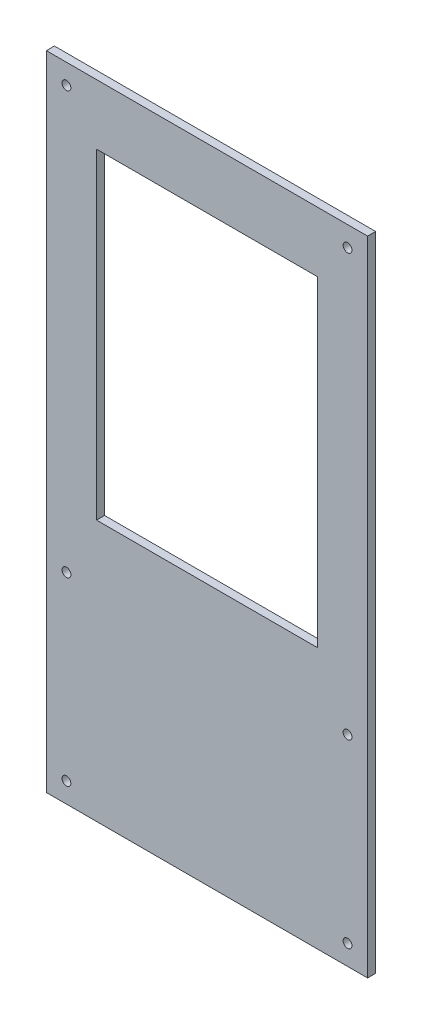
SolidWorks part; units mm, degrees
ref_plane "Plan de face" through (0, 0, 0) normal (0, 0, 1) x (1, 0, 0)
ref_plane "Plan de dessus" through (0, 0, 0) normal (0, 1, 0) x (1, 0, 0)
ref_plane "Plan de droite" through (0, 0, 0) normal (1, 0, 0) x (0, 0, -1)
sketch "Esquisse1" plane through (0, 0, 0) normal (0, 0, 1) x (1, 0, 0)
  line L0 (0, 220) -> (0, 0) construction
  line L1 (80, 220) -> (-80, 220)
  line L2 (80, 220) -> (80, -220)
  line L3 (80, -220) -> (-80, -220)
  line L4 (-80, 220) -> (-80, -220)
  line L5 (80, 220) -> (-80, -220) construction
  line L6 (80, -220) -> (-80, 220) construction
  line L7 (0, 0) -> (80, 0) construction
  line L8 (-70, 220) -> (-70, -220) construction
  line L9 (-70, -220) -> (-80, -210) construction
  line L10 (-80, -210) -> (80, -210) construction
  line L11 (-80, 210) -> (80, 210) construction
  line L12 (70, 220) -> (70, -220) construction
  line L14 (-55, 190) -> (55, 190)
  line L15 (-55, 190) -> (-55, 30)
  line L16 (-55, 30) -> (55, 30)
  line L17 (55, 190) -> (55, 30)
  line L18 (-55, 190) -> (55, 30) construction
  line L19 (-55, 30) -> (55, 190) construction
  circle A0 centre (70, 0) radius 2.2
  circle A1 centre (70, 210) radius 2.2
  circle A2 centre (70, -210) radius 2.2
  circle A3 centre (-70, 210) radius 2.2
  circle A4 centre (-70, 0) radius 2.2
  circle A5 centre (-70, -210) radius 2.2
  point P0 (0, 0)
  point P29 (0, 110)
  dimension "D5" = 4.4
  dimension "D6" = 4.4
  dimension "D7" = 4.4
  dimension "D1" = 160
  dimension "D2" = 440
  dimension "D3" = 10
  dimension "D4" = 10
  dimension "D8" = 110
  dimension "D9" = 160
  dimension "D10" = 20
extrude "Boss.-Extru.1" add sketch "Esquisse1" along normal blind 4
sketch "Esquisse2" plane through (0, 0, 4) normal (0, 0, 1) x (1, 0, 0)
  line L0 (80, -220) -> (80, 220) construction
  line L1 (-80, -220) -> (80, -220)
  line L2 (-80, -220) -> (-80, -100)
  line L3 (-80, -100) -> (80, -100)
  line L4 (80, -220) -> (80, -100)
  line L5 (-80, 220) -> (-80, -220) construction
  circle A0 centre (-70, -90) radius 2.2
  circle A1 centre (70, -90) radius 2.2
  dimension "D2" = 4.4
  dimension "D1" = 120
  dimension "D3" = 10
  dimension "D4" = 10
  dimension "D5" = 10
  dimension "D6" = 10
extrude "Enlèv. mat.-Extru.1" cut sketch "Esquisse2" against normal through all
